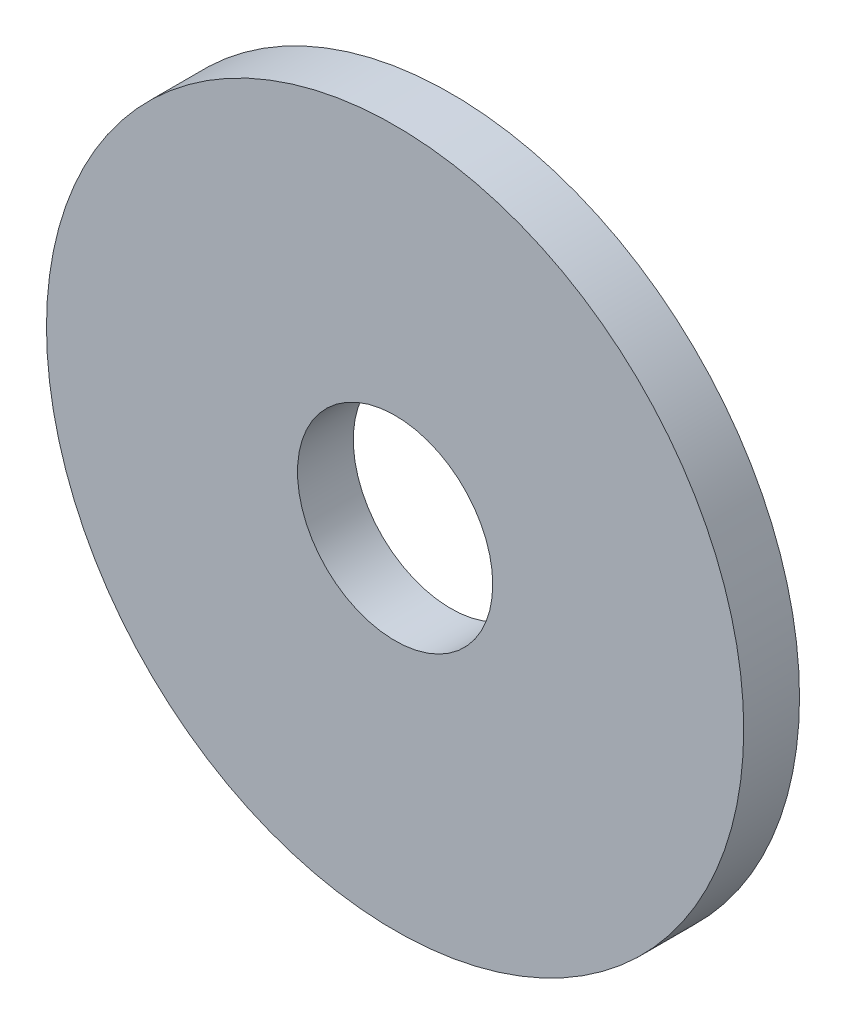
SolidWorks part; units mm, degrees
ref_plane "Plan1" through (0, 0, 0) normal (0, 0, 1) x (1, 0, 0)
ref_plane "Plan2" through (0, 0, 0) normal (0, 1, 0) x (1, 0, 0)
ref_plane "Plan3" through (0, 0, 0) normal (1, 0, 0) x (0, 0, -1)
sketch "Esquisse1" plane through (0, 0, 0) normal (0, 0, 1) x (1, 0, 0)
  circle A0 centre (0, 0) radius 3.5
  circle A1 centre (0, 0) radius 12.5
  dimension "D1" = 7
  dimension "D2" = 25
extrude "Base-Extrusion" add sketch "Esquisse1" along normal blind 2
